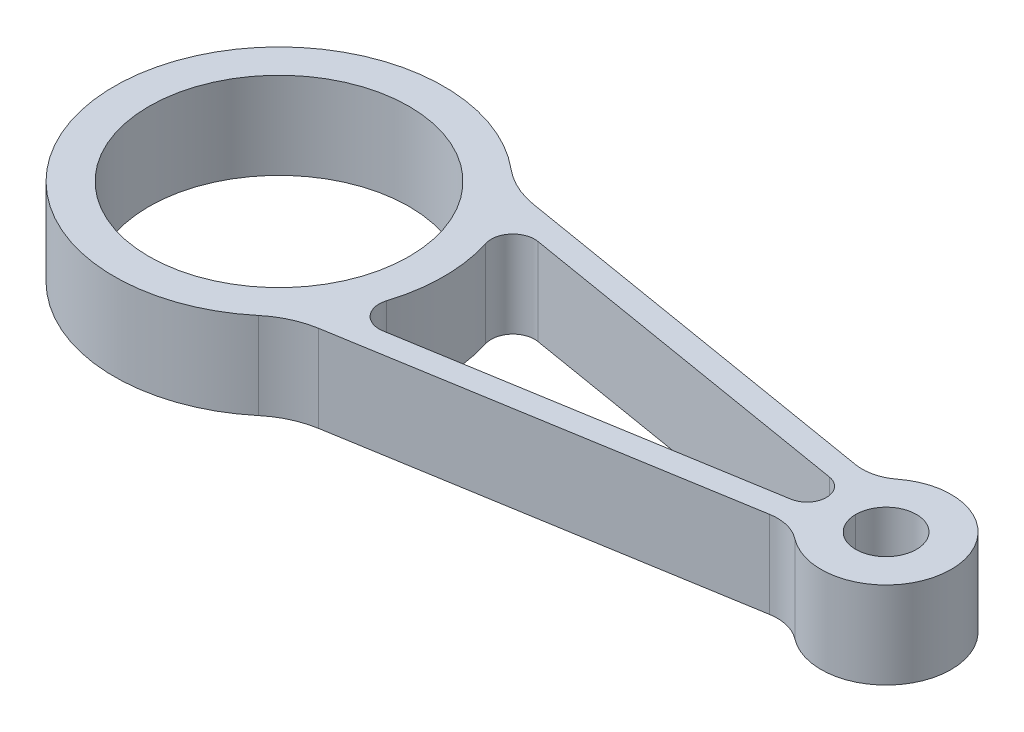
SolidWorks part; units mm, degrees
material "Plain Carbon Steel"
ref_plane "Front Plane" through (0, 0, 0) normal (0, 0, 1) x (1, 0, 0)
ref_plane "Top Plane" through (0, 0, 0) normal (0, 1, 0) x (1, 0, 0)
ref_plane "Right Plane" through (0, 0, 0) normal (1, 0, 0) x (0, 0, -1)
sketch "Sketch1" plane through (0, 0, 0) normal (0, 1, 0) x (1, 0, 0)
  line L0 (-26.0854, 0) -> (215.4296, 0) construction
  line L1 (27.9355, 25.7606) -> (128.0638, 9.0844)
  line L2 (27.9355, -25.7606) -> (128.0638, -9.0844)
  line L3 (133.0979, -1.1667) -> (136.7424, -0.5506) construction
  circle A6 centre (0, 0) radius 30
  circle A7 centre (140, 0) radius 7
  arc A8 (27.9355, 25.7606) -> (27.9355, -25.7606) centre (0, 0) ccw
  arc A9 (128.0638, -9.0844) -> (128.0638, 9.0844) centre (140, 0) ccw
  dimension "D1" = 60
  dimension "D2" = 14
  dimension "D3" = 76
  dimension "D4" = 30
  dimension "D5" = 140
extrude "Boss-Extrude1" add sketch "Sketch1" along normal mid plane 20
fillet "Fillet1" radius 20 2 edges at (27.9355, 0, -25.7606) (27.9355, 0, 25.7606)
fillet "Fillet2" radius 10 2 edges at (128.0638, 0, 9.0844) (128.0638, 0, -9.0844)
sketch "Sketch2" plane through (0, 10, 0) normal (0, 1, 0) x (1, 0, 0)
  line L0 (-70.4787, 0) -> (188.4371, 0) construction
  line L1 (41.8286, 17.871) -> (122.4784, 4.4389)
  line L2 (41.8286, -17.871) -> (122.4784, -4.4389)
  line L3 (123.0688, 9.9163) -> (33.9231, 24.7634) construction
  arc A0 (122.4784, 4.4389) -> (122.4784, -4.4389) centre (121.7391, 0) cw
  arc A1 (36.2389, 11.4344) -> (36.2389, -11.4344) centre (0, 0) cw
  circle A2 centre (0, 0) radius 30 construction
  arc A3 (36.2389, 11.4344) -> (41.8286, 17.871) centre (41.0071, 12.9389) cw
  arc A4 (36.2389, -11.4344) -> (41.8286, -17.871) centre (41.0071, -12.9389) ccw
  dimension "D1" = 4.5
  dimension "D3" = 8
  dimension "D4" = 5
  dimension "D2" = 5.5
extrude "Cut-Extrude1" cut sketch "Sketch2" against normal through all
split line "Split Line1"
